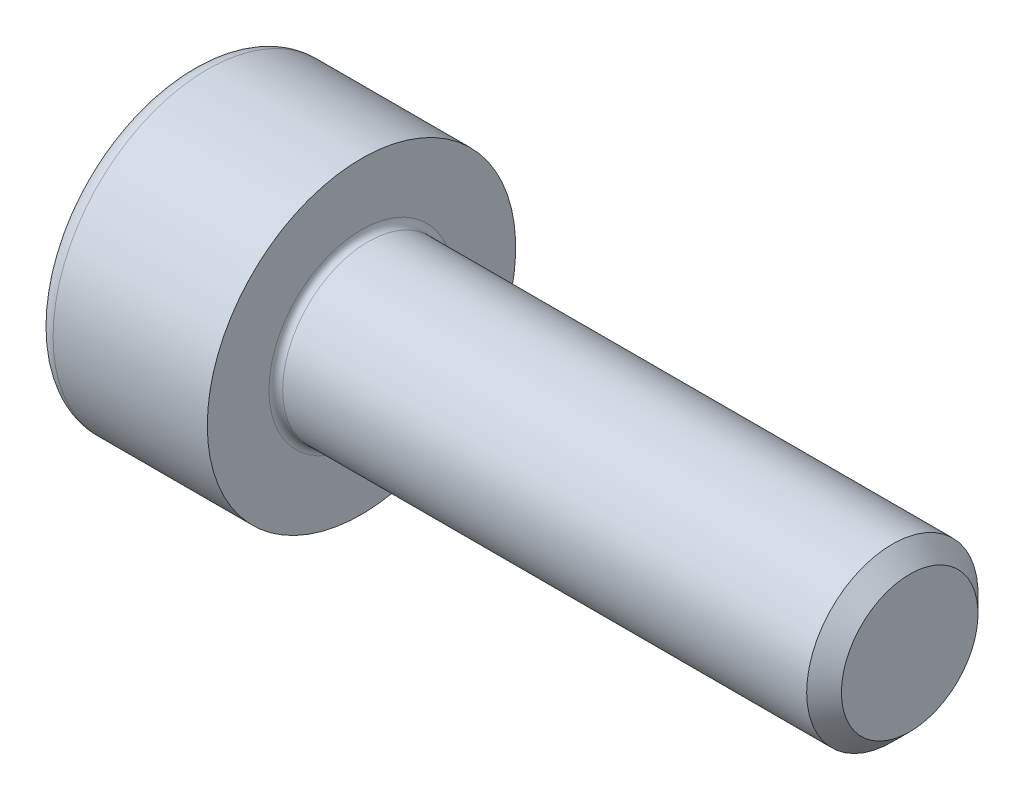
SolidWorks part; units mm, degrees
revolve "Base-Revolve" add sketch "BodySke"
sketch "BodySke" plane through (0, 0, 0) normal (0, 0, 1) x (1, 0, 0)
  line L0 (0, 0) -> (0, 2.25)
  line L1 (0, 2.25) -> (2.5, 2.25)
  line L2 (2.5, 2.25) -> (2.5, 1.25)
  line L3 (2.5, 1.25) -> (10.2465, 1.25)
  line L4 (10.5, 0.9965) -> (10.5, 0)
  line L5 (10.5, 0) -> (0, 0)
  line L6 (-31.75, 0) -> (127, 0) construction
  line L8 (10.5, 0.9965) -> (10.2465, 1.25)
  line L10 (10.5, -0.9965) -> (10.2465, -1.25) construction
  line L11 (2.95, 9.525) -> (2.95, 3.175) construction
  line L12 (2.5, 9.525) -> (2.5, 3.175) construction
  line L13 (-49.5, 9.525) -> (-49.5, 3.175) construction
  dimension "Head_ht" = 2.5
  dimension "Length" = 8
  dimension "Body_ch_ang" = 45
  dimension "Diameter" = 2.5
  dimension "Minor_dia" = 1.993
  dimension "Advance" = 0.45
  dimension "Thread_nom" = 8
  dimension "Thread_length" = 60
  dimension "Head_dia" = 4.5
cosmetic thread "ThreadCosmetic"
fillet "Fillet1" radius 0.1 1 edges at (2.5, 0, 1.25)
fillet "Fillet2" radius 0.25 1 edges at (0, 0, 2.25)
ref_plane "Plane1" through (0, 0, 0) normal (0, 0, 1) x (1, 0, 0)
ref_plane "Plane2" through (0, 0, 0) normal (0, 1, 0) x (1, 0, 0)
ref_plane "Plane3" through (0, 0, 0) normal (1, 0, 0) x (0, 0, -1)
sketch "Sketch2" plane through (0, 0, 0) normal (0, 0, 1) x (1, 0, 0)
  line L0 (0, 1.01) -> (1.1, 1.01)
  line L1 (1.1, 1.01) -> (1.6831, 0)
  line L2 (-31.75, 0) -> (127, 0) construction
  line L3 (1.6831, 0) -> (0, 0)
  line L4 (0, 0) -> (0, 1.01)
  line L6 (0, 0) -> (47.625, 0) construction
  dimension "D1" = 1.01
  dimension "D2" = 60
  dimension "Depth" = 1.1
revolve "Hex-PreBroach" cut sketch "Sketch2" angle 360 about L6
sketch "Sketch3" plane through (0, 0, 0) normal (-1, 0, 0) x (0, 0.5, 0.866)
  line L0 (0.5831, 1.01) -> (-0.5831, 1.01)
  line L1 (-0.5831, 1.01) -> (-1.1662, 0)
  line L2 (0.5831, 1.01) -> (1.1662, 0)
  line L3 (0.5831, -1.01) -> (1.1662, 0)
  line L4 (0.5831, -1.01) -> (-0.5831, -1.01)
  line L5 (-0.5831, -1.01) -> (-1.1662, 0)
  dimension "D1" = 1.01
  dimension "D2" = 1.01
  dimension "Hex_size" = 2.02
extrude "Hex" cut sketch "Sketch3" against normal blind 1.1
sketch "ThdSchSke" plane through (0, 0, 0) normal (0, 0, 1) x (1, 0, 0)
  line L0 (3.85, -0.9965) -> (3.6725, -1.25)
  line L1 (3.85, -0.9965) -> (4.0275, -1.25)
  line L2 (4.0275, -1.25) -> (4.0275, -1.5625)
  line L3 (-3.175, 0) -> (5.1513, 0) construction
  line L4 (0, 2) -> (0, -2) construction
  line L5 (4.0275, -1.5625) -> (3.6725, -1.5625)
  line L6 (3.6725, -1.5625) -> (3.6725, -1.25)
  dimension "Thread_minor" = 1.993
  dimension "Diameter" = 2.5
  dimension "Start" = 3.85
revolve "ThreadSchematic" [suppressed] cut sketch "ThdSchSke" angle 360 about L3
pattern_linear "ThdSchPat" [suppressed]
equation "\"D2@Sketch3\" = \"Hex_size@Sketch3\" / 2"
equation "\"D1@Sketch3\" = \"Hex_size@Sketch3\" / 2"
equation "\"D1@Sketch2\" = \"Hex_size@Sketch3\" / 2"
equation "\"Thread_minor@ThreadCosmetic\"  =  \"Minor_dia@BodySke\""
equation "\"Depth@Sketch2\" =  \"Key_eng@Hex\""
equation "\"Thread_length@ThreadCosmetic\" = ((sgn( (\"Length@BodySke\" - \"Advance@BodySke\" * 3.0) - \"Thread_nom@BodySke\" )-1)*( (\"Length@BodySke\" - \"Advance@BodySke\" * 3.0) - \"Thread_nom@BodySke\" ))/-2+ \"Thread_nom@BodySke\""
equation "\"Thread_minor@ThdSchSke\" = \"Minor_dia@BodySke\""
equation "\"Diameter@ThdSchSke\" = \"Diameter@BodySke\""
equation "\"Overcut@ThdSchSke\" = \"Diameter@BodySke\" * 1.25"
equation "\"Start@ThdSchSke\" = \"Head_ht@BodySke\" + \"Length@BodySke\" - \"Thread_length@ThreadCosmetic\"  '---Non-countersunk---"
equation "\"Num_threads@ThdSchPat\" = int( \"Thread_length@ThreadCosmetic\" / \"Advance@BodySke\" + 0.999 )  + 1"
equation "\"Advance@ThdSchPat\" = \"Thread_length@ThreadCosmetic\" /  (\"Num_threads@ThdSchPat\" - 1) 'relax it"
equation "\"Num_threads@ThdSchPat\" = \"Num_threads@ThdSchPat\" - sgn( \"Num_threads@ThdSchPat\" - 1) '---chamfered tips only---"
